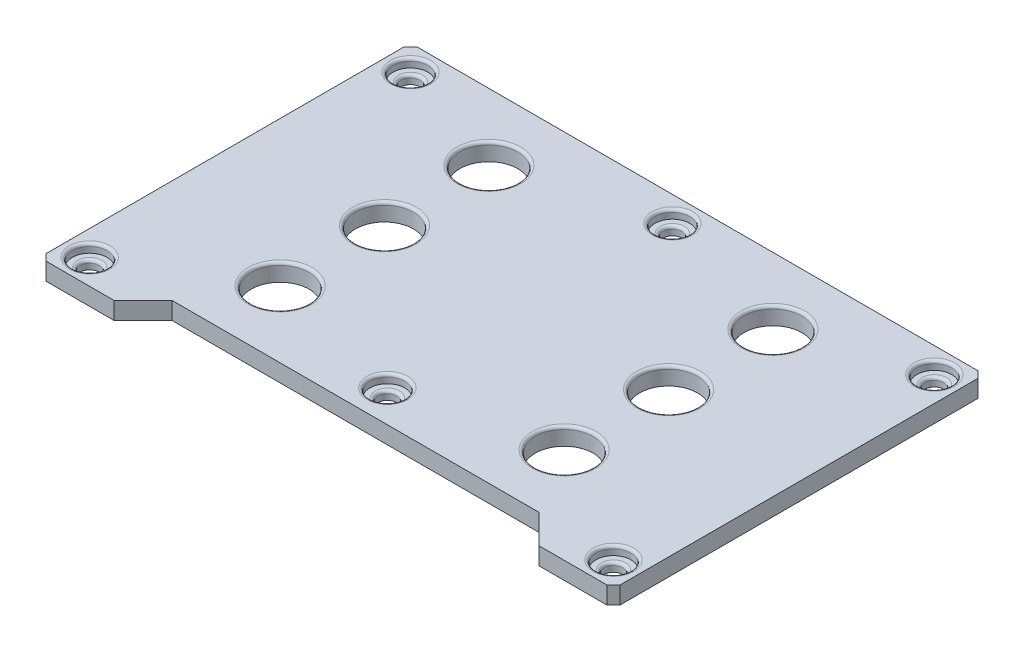
SolidWorks part; units mm, degrees
ref_plane "Front Plane" through (0, 0, 0) normal (0, 0, 1) x (1, 0, 0)
ref_plane "Top Plane" through (0, 0, 0) normal (0, 1, 0) x (1, 0, 0)
ref_plane "Right Plane" through (0, 0, 0) normal (1, 0, 0) x (0, 0, -1)
sketch "Sketch3" plane through (0, 0, 0) normal (0, 1, 0) x (1, 0, 0)
  line L0 (17.3523, -19.0435) -> (29.1096, -19.0435)
  line L5 (29.1096, -19.0435) -> (30.231, -17.9222)
  line L6 (30.231, -17.9222) -> (30.231, 43.8352)
  line L7 (30.231, 43.8352) -> (29.1096, 44.9565)
  line L8 (29.1096, 44.9565) -> (-67.6477, 44.9565)
  line L9 (-67.6477, 44.9565) -> (-68.769, 43.8352)
  line L10 (-68.769, 43.8352) -> (-68.769, -17.9222)
  line L11 (-68.769, -17.9222) -> (-67.6477, -19.0435)
  line L12 (-67.6477, -19.0435) -> (-55.8904, -19.0435)
  line L13 (-55.8904, -19.0435) -> (-50.8904, -14.0435)
  line L14 (-50.8904, -14.0435) -> (12.3523, -14.0435)
  line L15 (12.3523, -14.0435) -> (17.3523, -19.0435)
  line L16 (-19.269, 44.9565) -> (-19.269, -14.0435) construction
  line L17 (-68.769, 15.4565) -> (30.231, 15.4565) construction
  line L18 (-43.769, 44.9565) -> (-43.769, -14.0435) construction
  circle A0 centre (-64.439, 40.6265) radius 1.6
  circle A1 centre (-64.439, -14.7135) radius 1.6
  circle A2 centre (25.901, 40.6265) radius 1.6
  circle A3 centre (25.901, -14.7135) radius 1.6
  circle A4 centre (-43.769, 33.4565) radius 5
  circle A5 centre (-43.769, 15.4565) radius 5
  circle A6 centre (-43.769, -2.5435) radius 5
  circle A7 centre (5.231, -2.5435) radius 5
  circle A8 centre (5.231, 15.4565) radius 5
  circle A9 centre (5.231, 33.4565) radius 5
  circle A10 centre (-19.269, 40.6265) radius 1.6
  circle A11 centre (-19.269, -8.5435) radius 1.6
  point P22 (-19.269, 15.4565)
  point P26 (-19.269, 15.4565)
  point P28 (-43.769, 15.4565)
  point P46 (-19.269, 40.6265)
  point P47 (-19.269, -8.5435)
  dimension "D1" = 3.2
  dimension "D4" = 3.2
  dimension "D7" = 3.2
  dimension "D8" = 3.2
  dimension "D13" = 10
  dimension "D14" = 10
  dimension "D15" = 10
  dimension "D19" = 3.2
  dimension "D20" = 3.2
  dimension "D2" = 4.33
  dimension "D3" = 4.33
  dimension "D5" = 4.33
  dimension "D6" = 4.33
  dimension "D9" = 4.33
  dimension "D10" = 4.33
  dimension "D11" = 4.33
  dimension "D12" = 4.33
  dimension "D16" = 25
  dimension "D17" = 18
  dimension "D18" = 18
  dimension "D21" = 4.33
  dimension "D22" = 5.5
extrude "Boss-Extrude1" add sketch "Sketch3" against normal blind 3
sketch "Sketch4" plane through (0, 0, 0) normal (0, 1, 0) x (1, 0, 0)
  circle A0 centre (-64.439, 40.6265) radius 3
  circle A1 centre (-64.439, -14.7135) radius 3
  circle A2 centre (25.901, 40.6265) radius 3
  circle A3 centre (25.901, -14.7135) radius 3
  circle A4 centre (-19.269, 40.6265) radius 3
  circle A5 centre (-19.269, -8.5435) radius 3
  dimension "D1" = 6
  dimension "D2" = 6
  dimension "D3" = 6
  dimension "D4" = 6
  dimension "D5" = 6
  dimension "D6" = 6
extrude "Cut-Extrude1" cut sketch "Sketch4" against normal blind 1.5
fillet "Fillet1" radius 0.5 18 edges at (-64.439, -1.5, 16.3135) (-64.439, 0, 17.7135) (25.901, 0, 17.7135) (25.901, -1.5, 16.3135) (25.901, -1.5, -39.0265) (25.901, 0, -37.6265) (-64.439, -1.5, -39.0265) (-64.439, 0, -37.6265) (-19.269, -1.5, 10.1435) (-19.269, 0, 11.5435) (-19.269, -1.5, -39.0265) (-19.269, 0, -37.6265) (5.231, 0, -38.4565) (5.231, 0, -20.4565) (5.231, 0, -2.4565) (-43.769, 0, 7.5435) (-43.769, 0, -10.4565) (-43.769, 0, -28.4565)
